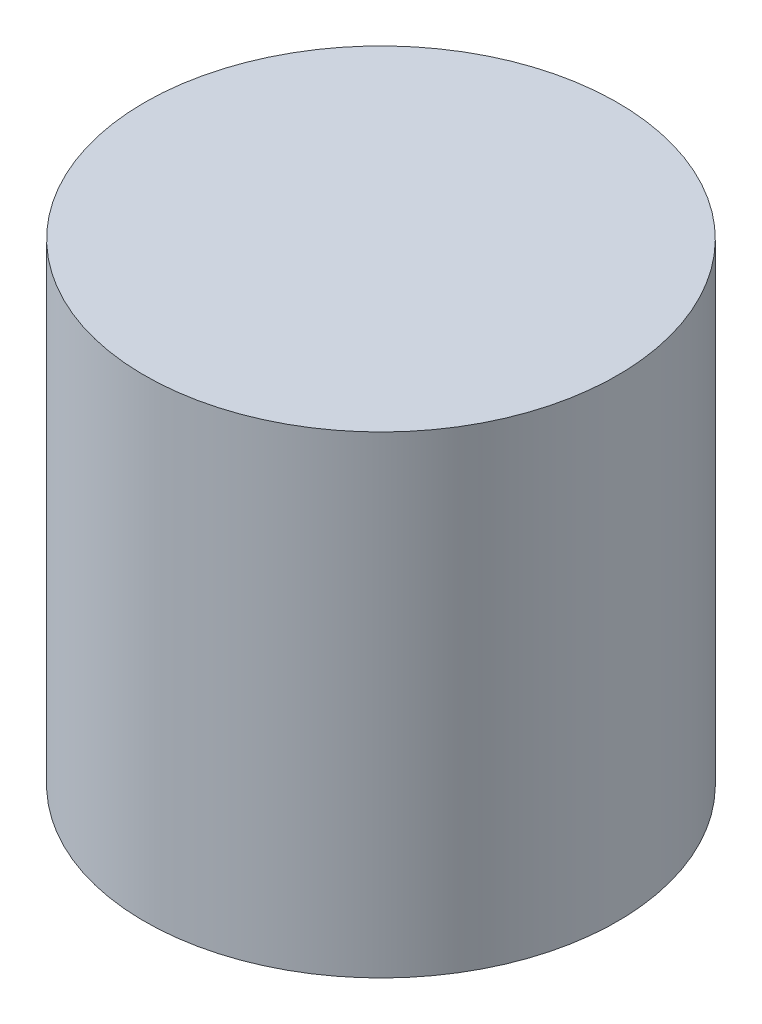
SolidWorks part; units mm, degrees
material "Acrylic (Medium-high impact)"
ref_plane "Front Plane" through (0, 0, 0) normal (0, 0, 1) x (1, 0, 0)
ref_plane "Top Plane" through (0, 0, 0) normal (0, 1, 0) x (1, 0, 0)
ref_plane "Right Plane" through (0, 0, 0) normal (1, 0, 0) x (0, 0, -1)
sketch "Sketch1" plane through (0, 0, 0) normal (0, 0, 1) x (1, 0, 0)
  line L0 (0, 50.8) -> (0, -50.8) construction
  line L1 (0, -50.8) -> (50.8, -50.8)
  line L2 (50.8, -50.8) -> (50.8, 50.8)
  line L3 (50.8, 50.8) -> (0, 50.8)
  line L4 (0, 44.45) -> (44.45, 44.45)
  line L5 (44.45, 44.45) -> (44.45, -44.45)
  line L6 (44.45, -44.45) -> (0, -44.45)
  dimension "D1" = 101.6
  dimension "D2" = 50.8
  dimension "D3" = 6.35
  dimension "D4" = 6.35
  dimension "D5" = 6.35
revolve "Revolve1" add sketch "Sketch1" angle 360 about L0
